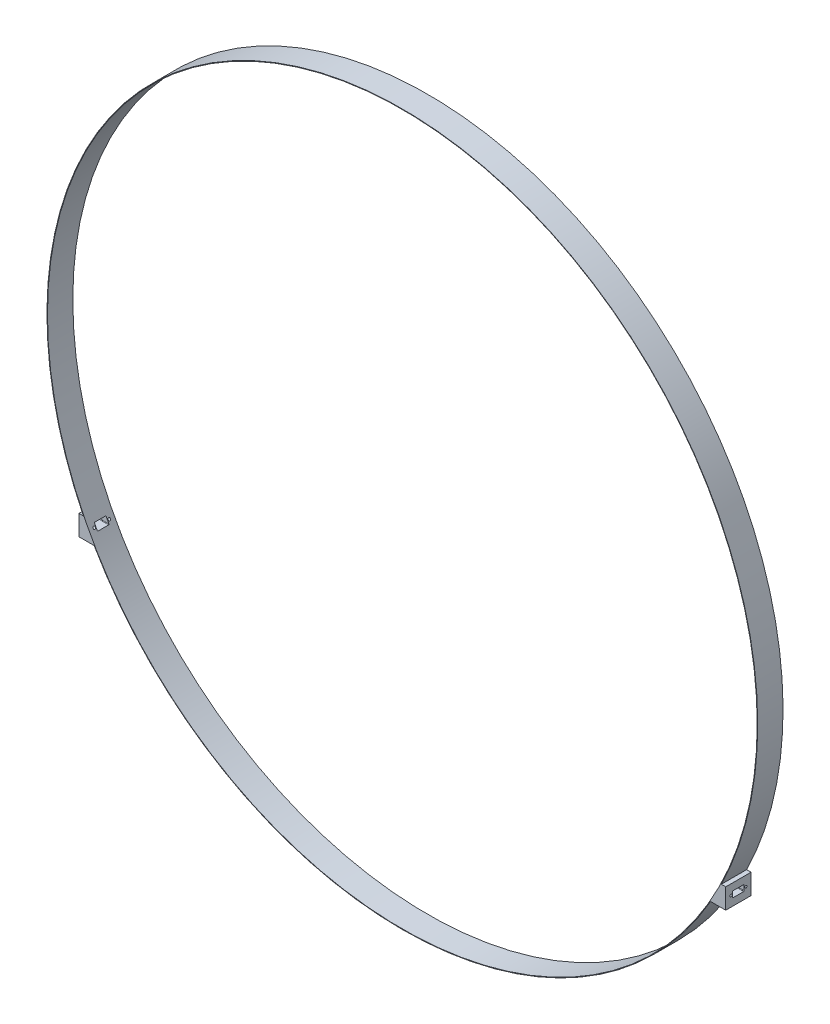
SolidWorks part; units mm, degrees
material "Balsa"
ref_plane "Front Plane" through (0, 0, 0) normal (0, 0, 1) x (1, 0, 0)
ref_plane "Top Plane" through (0, 0, 0) normal (0, 1, 0) x (1, 0, 0)
ref_plane "Right Plane" through (0, 0, 0) normal (1, 0, 0) x (0, 0, -1)
sketch "Sketch1" plane through (0, 0, 0) normal (0, 0, 1) x (1, 0, 0)
  circle A0 centre (0, 0) radius 700
  circle A1 centre (0, 0) radius 701
  dimension "D1" = 1400
  dimension "D2" = 1402
extrude "Extrude1" add sketch "Sketch1" against normal blind 50
sketch "Sketch4" plane through (0, 0, 0) normal (0, 0, 1) x (1, 0, 0)
  line L0 (-629.2217, -309) -> (-637.9474, -309)
  line L1 (-637.9474, -309) -> (-637.9474, -349)
  line L2 (-637.9474, -349) -> (-607.9474, -349)
  circle A0 centre (0, 0) radius 701 construction
  arc A1 (-629.2217, -309) -> (-607.9474, -349) centre (0, 0) ccw
  point P2 (-637.9474, -329)
  dimension "D1" = 40
  dimension "D2" = 30
  dimension "D3" = 329
extrude "Extrude4" add sketch "Sketch4" against normal blind 50
mirror "Mirror1" about plane through (0, 0, 0) normal (1, 0, 0) of "Extrude4"
sketch "Sketch5" plane through (637.9474, 0, 0) normal (1, 0, 0) x (0, 0, -1)
  line L0 (14.5, -322.8399) -> (35.5, -322.8399)
  line L1 (13.5, -323.8399) -> (13.5, -333.8399)
  line L2 (14.5, -334.8399) -> (35.5, -334.8399)
  line L3 (36.5, -323.8399) -> (36.5, -333.8399)
  line L4 (50, -309) -> (50, -349) construction
  line L5 (50, -349) -> (0, -349) construction
  circle A0 centre (10.3879, -328.8399) radius 2.25
  circle A1 centre (39.7879, -328.8399) radius 2.25
  arc A2 (14.5, -322.8399) -> (13.5, -323.8399) centre (14.5, -323.8399) ccw
  arc A3 (14.5, -334.8399) -> (13.5, -333.8399) centre (14.5, -333.8399) cw
  arc A4 (35.5, -322.8399) -> (36.5, -323.8399) centre (35.5, -323.8399) cw
  arc A5 (35.5, -334.8399) -> (36.5, -333.8399) centre (35.5, -333.8399) ccw
  point P16 (25, -334.8399)
  point P17 (13.5, -328.8399)
  dimension "D1" = 4.5
  dimension "D2" = 4.5
  dimension "D5" = 1
  dimension "D3" = 29.4
  dimension "D4" = 6
  dimension "D6" = 25
  dimension "D7" = 21
  dimension "D8" = 12
  dimension "D9" = 20.1601
extrude "Extrude5" cut sketch "Sketch5" against normal blind 1500
